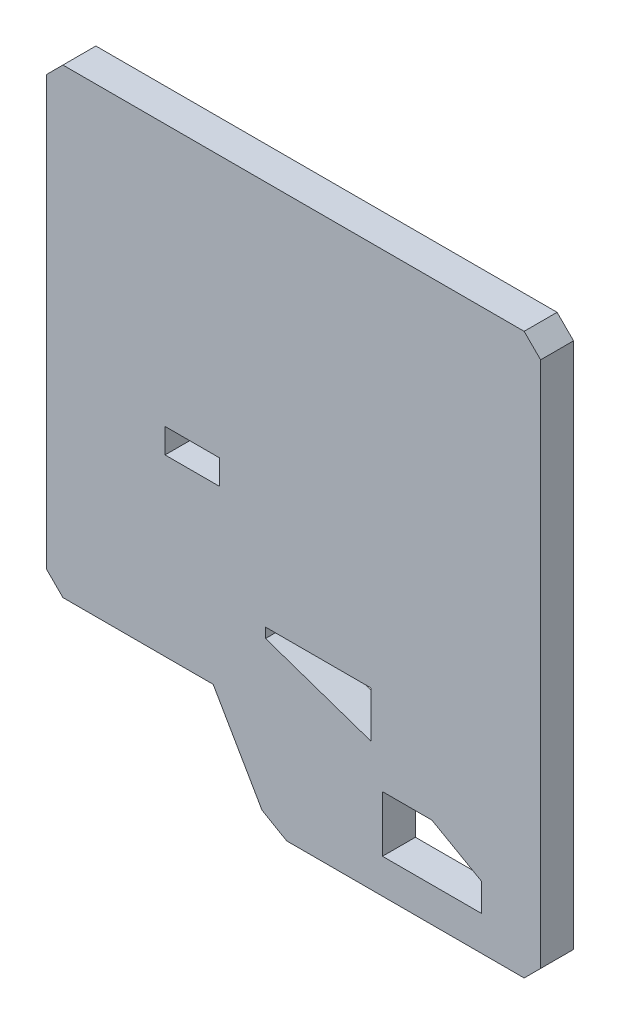
SolidWorks part; units mm, degrees
material "Plain Carbon Steel"
ref_plane "Front" through (0, 0, 0) normal (0, 0, 1) x (1, 0, 0)
ref_plane "Top" through (0, 0, 0) normal (0, 1, 0) x (1, 0, 0)
ref_plane "Right" through (0, 0, 0) normal (1, 0, 0) x (0, 0, -1)
sketch "Sketch2" plane through (0, 0, 0) normal (0, 0, 1) x (1, 0, 0)
  line L0 (-140, -110) -> (-48.7821, -110)
  line L1 (140, 170) -> (-140, 170)
  line L2 (150, 160) -> (150, -160)
  line L3 (140, -170) -> (-4.1411, -170)
  line L4 (-150, 160) -> (-150, -100)
  line L5 (150, 170) -> (-97.0588, -110) construction
  line L6 (150, -170) -> (-150, 170) construction
  line L7 (-48.7821, -110) -> (-19.1411, -161.3397)
  line L8 (84, -115) -> (114, -132)
  line L9 (54, -149) -> (114, -149)
  line L10 (54, -149) -> (54, -115)
  line L11 (54, -115) -> (84, -115)
  line L12 (114, -149) -> (114, -132)
  line L13 (-140, 170) -> (-150, 160)
  line L14 (150, 160) -> (140, 170)
  line L15 (47, -92) -> (-17, -70)
  line L16 (-17, -64) -> (47, -64)
  line L17 (-17, -64) -> (-17, -70)
  line L19 (47, -64) -> (47, -92)
  line L20 (-17, -64) -> (47, -92) construction
  line L21 (150, -160) -> (140, -170)
  line L22 (-78, 11) -> (-45, 11)
  line L23 (-78, 11) -> (-78, -4)
  line L24 (-78, -4) -> (-45, -4)
  line L25 (-45, 11) -> (-45, -4)
  line L26 (-78, 11) -> (-45, -4) construction
  line L27 (-78, -4) -> (-45, 11) construction
  line L28 (-19.1411, -161.3397) -> (-4.1411, -170)
  line L29 (-150, -100) -> (-140, -110)
  point P0 (0, 0)
  point P6 (-150, -110)
  point P8 (-14.1411, -170)
  point P21 (-61.5, 3.5)
  dimension "D1" = 300
  dimension "D2" = 340
  dimension "D3" = 280
  dimension "D4" = 240
  dimension "D5" = 150
  dimension "D6" = 135.8589
  dimension "D7" = 21
  dimension "D8" = 34
  dimension "D9" = 23
  dimension "D10" = 22
  dimension "D11" = 6
  dimension "D12" = 60
  dimension "D13" = 15
  dimension "D14" = 36
  dimension "D15" = 30
  dimension "D16" = 30
  dimension "D17" = 17
  dimension "D18" = 103
  dimension "D19" = 64
  dimension "D20" = 33
  dimension "D21" = 195
extrude "Boss-Extrude1" add sketch "Sketch2" along normal blind 20
sketch "Sketch8" plane through (0, -110, 0) normal (0, -1, 0) x (1, 0, 0)
  line L0 (-145, 0) -> (-145, -80)
  line L1 (-140, 0) -> (-48.7821, 0) construction
  line L2 (-35, 0) -> (-35, -40)
  line L3 (-145, 0) -> (-35, 0)
  line L4 (-150, 20) -> (-150, 0) construction
  line L5 (-35, -40) -> (10, -40)
  line L6 (10, -120) -> (-52.2508, -120)
  circle A0 centre (-90, -80) radius 40
  arc A1 (-145, -80) -> (-52.2508, -120) centre (-90, -80) ccw
  circle A2 centre (10, -80) radius 15
  arc A3 (10, -120) -> (10, -40) centre (10, -80) ccw
  dimension "D4" = 80
  dimension "D5" = 30
  dimension "D6" = 80
  dimension "D1" = 110
  dimension "D2" = 55
  dimension "D3" = 5
  dimension "D7" = 100
  dimension "D8" = 40
extrude "Boss-Extrude3" add sketch "Sketch8" against normal up to vertex (10 mm away)
pattern_linear "LPattern1" count 2 spacing 70 along (0, 1, 0) of "Boss-Extrude3"
